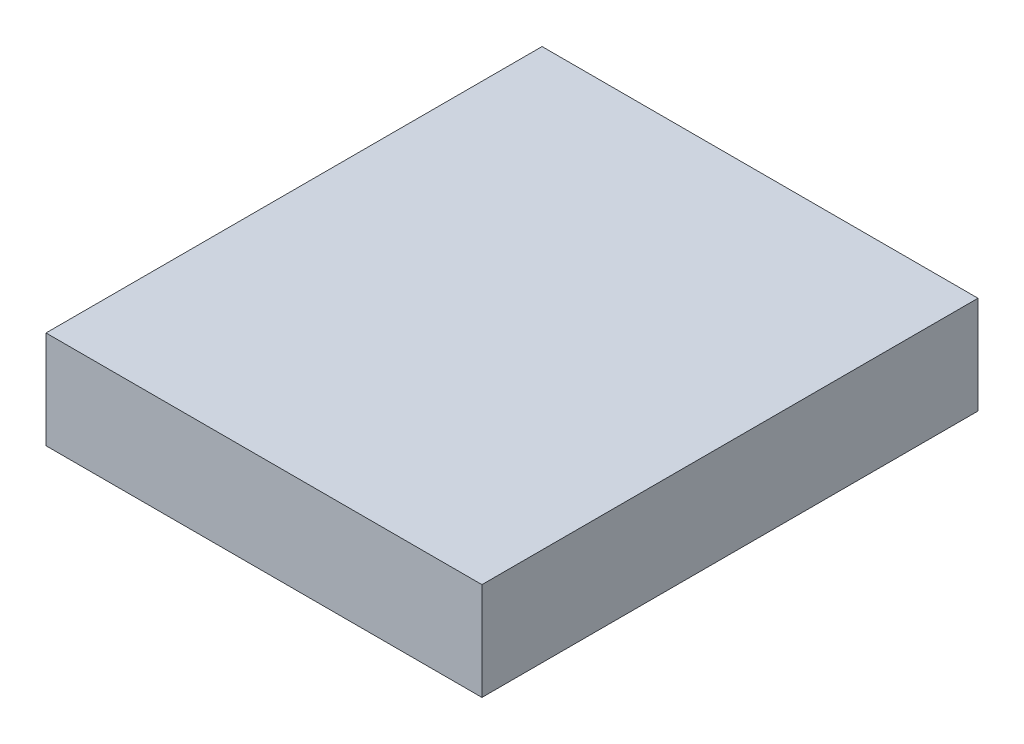
SolidWorks part; units mm, degrees
ref_plane "Front Plane" through (0, 0, 0) normal (0, 0, 1) x (1, 0, 0)
ref_plane "Top Plane" through (0, 0, 0) normal (0, 1, 0) x (1, 0, 0)
ref_plane "Right Plane" through (0, 0, 0) normal (1, 0, 0) x (0, 0, -1)
sketch "Sketch1" plane through (0, 0, 0) normal (0, 1, 0) x (1, 0, 0)
  line L1 (0, 0) -> (736.6, 0)
  line L2 (0, 0) -> (0, 838.2)
  line L3 (0, 838.2) -> (736.6, 838.2)
  line L4 (736.6, 0) -> (736.6, 838.2)
  dimension "D1" = 838.2
  dimension "D2" = 736.6
extrude "Boss-Extrude1" add sketch "Sketch1" along normal blind 165.1
